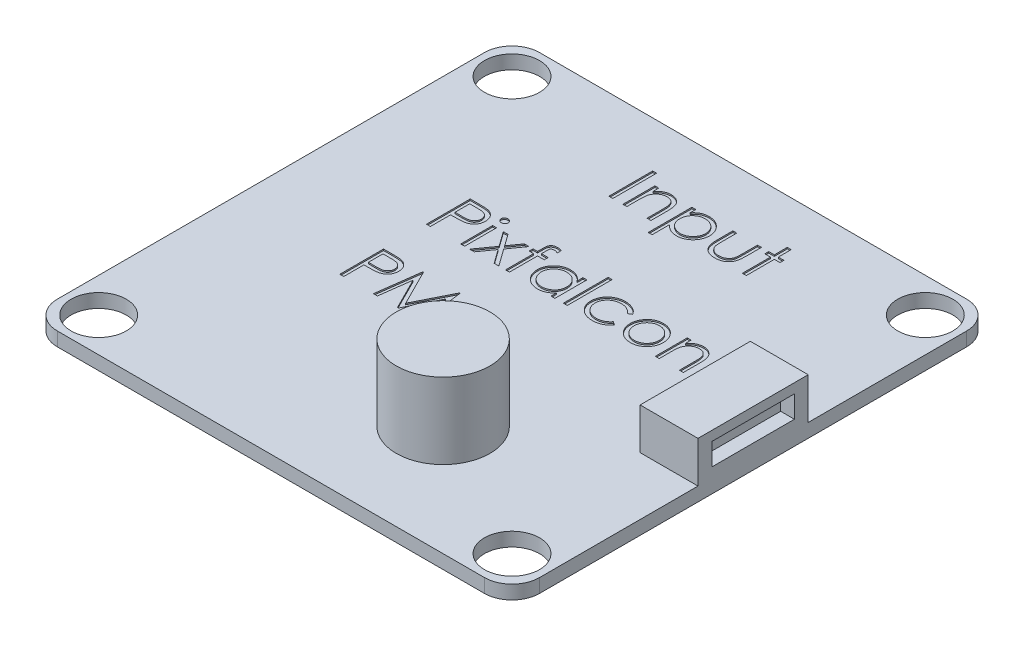
SolidWorks part; units mm, degrees
ref_plane "Front Plane" through (0, 0, 0) normal (0, 0, 1) x (1, 0, 0)
ref_plane "Top Plane" through (0, 0, 0) normal (0, 1, 0) x (1, 0, 0)
ref_plane "Right Plane" through (0, 0, 0) normal (1, 0, 0) x (0, 0, -1)
sketch "Sketch1" plane through (0, 0, 0) normal (0, 1, 0) x (1, 0, 0)
  line L0 (0, 17.5) -> (0, -17.5) construction
  line L1 (-15.5, 17.5) -> (15.5, 17.5)
  line L2 (-17.5, 15.5) -> (-17.5, -15.5)
  line L3 (-15.5, -17.5) -> (15.5, -17.5)
  line L4 (17.5, 15.5) -> (17.5, -15.5)
  line L5 (-17.5, 17.5) -> (17.5, -17.5) construction
  line L6 (-17.5, -17.5) -> (17.5, 17.5) construction
  line L7 (-17.5, 0) -> (17.5, 0) construction
  circle A0 centre (15, 15) radius 2
  circle A1 centre (15, -15) radius 2
  circle A2 centre (-15, -15) radius 2
  circle A3 centre (-15, 15) radius 2
  arc A4 (15.5, -17.5) -> (17.5, -15.5) centre (15.5, -15.5) ccw
  arc A5 (-17.5, -15.5) -> (-15.5, -17.5) centre (-15.5, -15.5) ccw
  arc A6 (15.5, 17.5) -> (17.5, 15.5) centre (15.5, 15.5) cw
  arc A7 (-15.5, 17.5) -> (-17.5, 15.5) centre (-15.5, 15.5) ccw
  point P0 (0, 0)
  point P21 (0, 0)
  dimension "D3" = 4
  dimension "D6" = 2
  dimension "D1" = 35
  dimension "D2" = 35
  dimension "D4" = 15
  dimension "D5" = 4
extrude "Boss-Extrude1" add sketch "Sketch1" along normal blind 1
sketch "Sketch2" plane through (0, 1, 0) normal (0, 1, 0) x (1, 0, 0)
  line L0 (17.5, 0) -> (-17.5, 0) construction
  line L1 (17.5, -15.5) -> (17.5, 15.5) construction
  line L2 (-17.5, 15.5) -> (-17.5, -15.5) construction
  line L4 (17.5, 4) -> (13.3, 4)
  line L5 (17.5, 4) -> (17.5, -4)
  line L6 (17.5, -4) -> (13.3, -4)
  line L7 (13.3, 4) -> (13.3, -4)
  dimension "D1" = 4
  dimension "D2" = 4
  dimension "D3" = 4.2
extrude "Boss-Extrude2" add sketch "Sketch2" along normal blind 3
sketch "Sketch3" plane through (17.5, 0, 0) normal (1, 0, 0) x (0, 0, -1)
  line L0 (-4, 2.5) -> (4, 2.5) construction
  line L1 (-4, 4) -> (-4, 1) construction
  line L2 (4, 4) -> (4, 1) construction
  line L3 (-4, 4) -> (4, 4) construction
  line L4 (-3, 3.3) -> (3, 3.3)
  line L5 (-3, 3.3) -> (-3, 1.7)
  line L6 (-3, 1.7) -> (3, 1.7)
  line L7 (3, 3.3) -> (3, 1.7)
  line L8 (-3, 3.3) -> (3, 1.7) construction
  line L9 (-3, 1.7) -> (3, 3.3) construction
  point P6 (0, 2.5)
  dimension "D1" = 0.7
  dimension "D2" = 1
extrude "Cut-Extrude1" cut sketch "Sketch3" against normal blind 1
sketch "Sketch4" plane through (0, 1, 0) normal (0, 1, 0) x (1, 0, 0)
  line L0 (17.5, -15.5) -> (17.5, -4) construction
  line L1 (-15.5, -17.5) -> (15.5, -17.5) construction
  circle A0 centre (4.5, -9.5) radius 3.4
  dimension "D1" = 6.8
  dimension "D2" = 13
  dimension "D3" = 8
extrude "Boss-Extrude3" add sketch "Sketch4" along normal blind 5.5
sketch "Sketch5" plane through (0, 1, 0) normal (0, 1, 0) x (1, 0, 0)
  text T0 "Pixfalcon\r\nPM"
  text T1 "Input"
extrude "Cut-Extrude2" cut sketch "Sketch5" against normal blind 0.1
